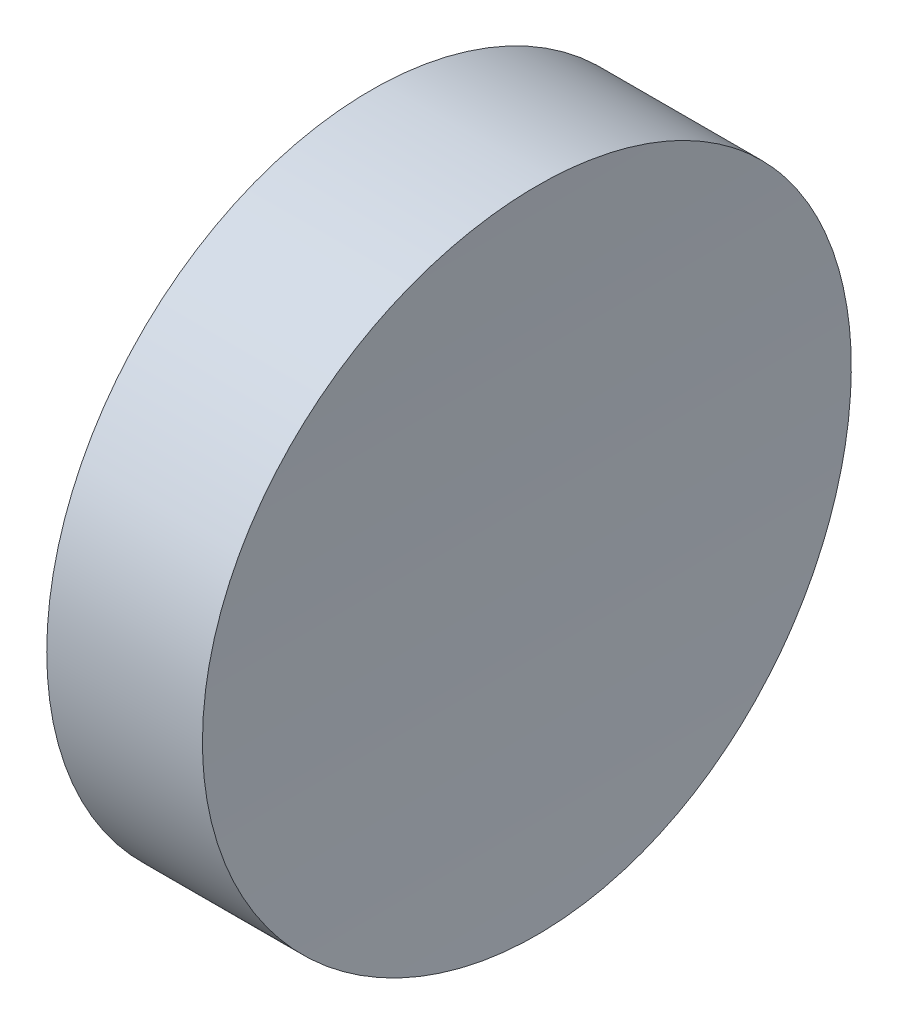
SolidWorks part; units mm, degrees
ref_plane "前视基准面" through (0, 0, 0) normal (0, 0, 1) x (1, 0, 0)
ref_plane "上视基准面" through (0, 0, 0) normal (0, 1, 0) x (1, 0, 0)
ref_plane "右视基准面" through (0, 0, 0) normal (1, 0, 0) x (0, 0, -1)
sketch "草图1" plane through (0, 0, 0) normal (1, 0, 0) x (0, 0, -1)
  circle A0 centre (0, 0) radius 6.25
  dimension "D1" = 12.5
extrude "凸台-拉伸1" add sketch "草图1" along normal blind 10
sketch "草图2" plane through (0, 0, 0) normal (0, 0, 1) x (1, 0, 0)
  line L0 (0, 0) -> (103, 0) construction
  line L1 (0, 0) -> (3, 0) construction
  circle A0 centre (103, 0) radius 100
  dimension "D1" = 200
  dimension "D2" = 3
extrude "切除-拉伸1" cut sketch "草图2" against normal through all both and the other way through all
